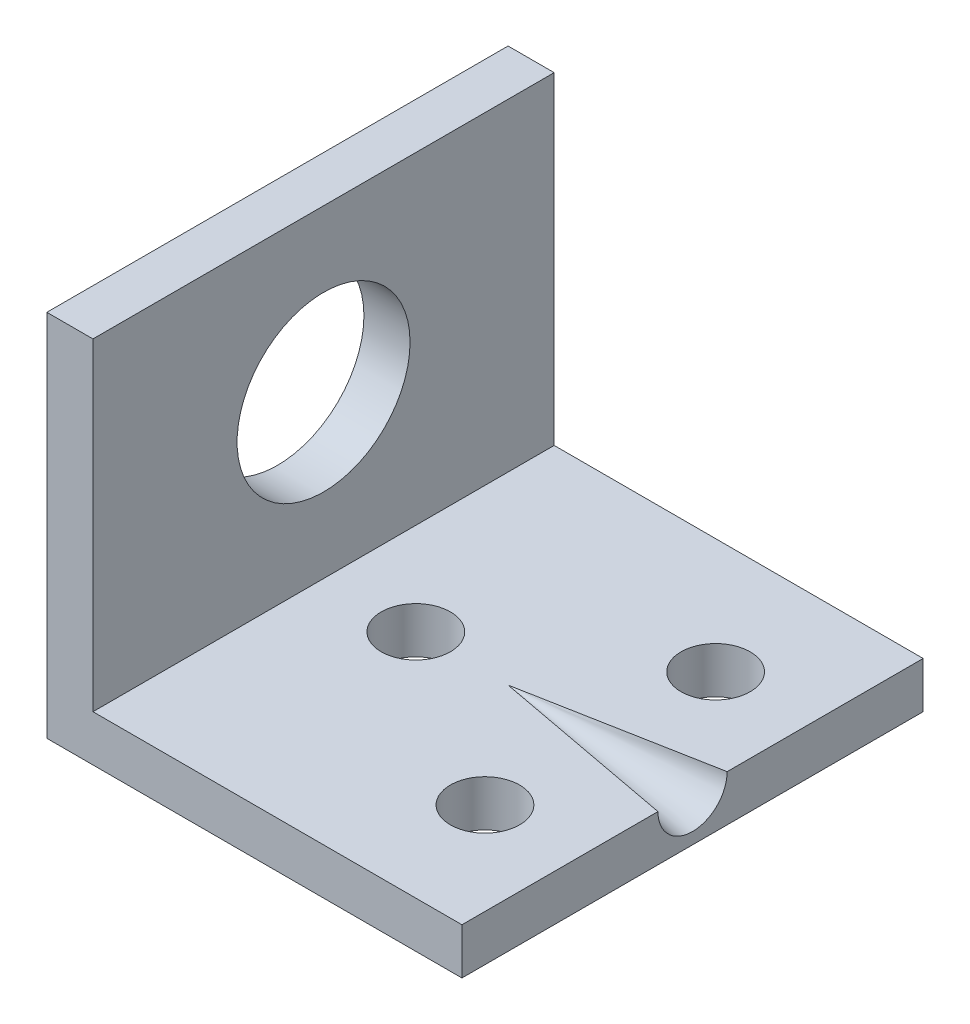
SolidWorks part; units mm, degrees
ref_plane "前视基准面" through (0, 0, 0) normal (0, 0, 1) x (1, 0, 0)
ref_plane "上视基准面" through (0, 0, 0) normal (0, 1, 0) x (1, 0, 0)
ref_plane "右视基准面" through (0, 0, 0) normal (1, 0, 0) x (0, 0, -1)
sketch "草图1" plane through (0, 0, 0) normal (0, 1, 0) x (1, 0, 0)
  line L0 (-3, 0) -> (-3, -10)
  line L1 (-3, -10) -> (15, -10)
  line L2 (15, -10) -> (15, 10)
  line L3 (15, 10) -> (-3, 10)
  line L4 (-3, 10) -> (-3, 0)
  line L5 (-3, 0) -> (3, 0)
  line L6 (3, 0) -> (3, 5)
  line L7 (3, 0) -> (11, 0)
  line L8 (11, 0) -> (11, 5)
  circle A3 centre (3, 0) radius 1.5
  circle A4 centre (11, 5) radius 1.5
  circle A5 centre (11, -5) radius 1.5
extrude "凸台-拉伸1" add sketch "草图1" along normal blind 2
sketch "草图2" plane through (0, 2, 0) normal (0, 1, 0) x (1, 0, 0)
  line L0 (-3, 10) -> (-1, 10)
  line L1 (15, 10) -> (-3, 10) construction
  line L2 (-1, 10) -> (-1, -10)
  line L3 (-3, -10) -> (15, -10) construction
  line L4 (-1, -10) -> (-3, -10)
  line L5 (-3, -10) -> (-3, 10)
extrude "凸台-拉伸2" add sketch "草图2" along normal blind 14
ref_plane "基准面1" through (-1, 2, -10) normal (0, 0, -1) x (-1, 0, 0)
sketch "草图4" plane through (-1, 0, 0) normal (1, 0, 0) x (0, 0, -1)
  line L0 (0, 2) -> (0, 9)
  line L1 (-10, 2) -> (10, 2) construction
  circle A0 centre (0, 9) radius 3.75
extrude "切除-拉伸1" cut sketch "草图4" against normal blind 10 contours A0
sketch "草图5" plane through (15, 0, 0) normal (1, 0, 0) x (0, 0, -1)
  line L0 (-10, 2) -> (10, 2) construction
  circle A0 centre (0, 2) radius 1.5
sketch "草图6" plane through (0, 2, 0) normal (0, 1, 0) x (1, 0, 0)
  line L0 (3, 0) -> (7, 0)
sketch "草图7" plane through (0, 2, 0) normal (0, 1, 0) x (1, 0, 0)
  line L0 (7, 0) -> (15, 0)
  line L1 (15, -1.5) -> (15, 1.5) construction
  line L2 (15, 0) -> (15, 1.5)
  line L3 (15, 1.5) -> (7, 0)
revolve "切除-旋转1" cut sketch "草图7" angle 360 about L0
